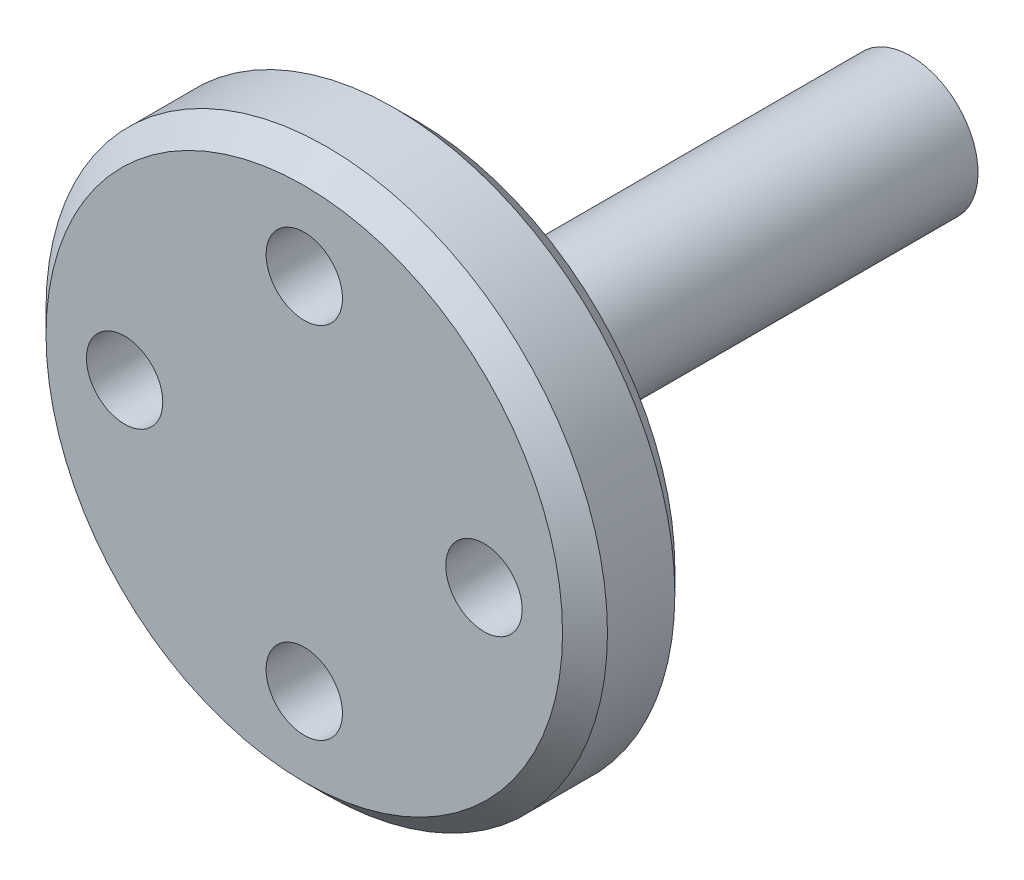
SolidWorks part; units mm, degrees
material "1060 Alloy"
ref_plane "Front Plane" through (0, 0, 0) normal (0, 0, 1) x (1, 0, 0)
ref_plane "Top Plane" through (0, 0, 0) normal (0, 1, 0) x (1, 0, 0)
ref_plane "Right Plane" through (0, 0, 0) normal (1, 0, 0) x (0, 0, -1)
sketch "Sketch1" plane through (0, 0, 0) normal (1, 0, 0) x (0, 0, -1)
  line L0 (0, 0) -> (0, 12.5)
  line L1 (0, 12.5) -> (5, 12.5)
  line L2 (5, 12.5) -> (5, 3)
  line L3 (5, 3) -> (27, 3)
  line L4 (27, 3) -> (27, 0)
  line L5 (27, 0) -> (0, 0)
  dimension "D1" = 12.5
  dimension "D2" = 22
  dimension "D3" = 3
  dimension "D4" = 5
revolve "Revolve1" add sketch "Sketch1" angle 360 about L5
sketch "Sketch2" plane through (0, 0, 0) normal (0, 0, 1) x (1, 0, 0)
  point P0 (8, 0)
  dimension "D1" = 8
hole_wizard "M3 Clearance Hole1" positions "3DSketch1" profile "Sketch3" hole size "M3" standard "ISO"
sketch3d "3DSketch1"
  point P0 (8, 0, 0)
sketch "Sketch3" plane through (8, 0, 0) normal (1, 0, 0) x (0, -1, 0)
  line L0 (0, 0) -> (0, 6.0205)
  line L1 (0, 6.0205) -> (1.7, 4.999)
  line L2 (1.7, 4.999) -> (1.7, 0)
  line L5 (1.7, 0) -> (0, 0)
  line L10 (0, 6.0205) -> (-1.7, 4.999) construction
  line L11 (0, -6.35) -> (0, 107.95) construction
  dimension "Hole Dia." = 3.4
  dimension "Hole Depth" = 4.999
  dimension "Drill Angle" = 118
pattern_circular "CirPattern1" count 4 over 360 about axis through (0, 0, 0) along (0, 0, 1) of "M3 Clearance Hole1"
chamfer "Chamfer1" distance 1 angle 45 2 edges at (0, 12.5, -5) (0, 12.5, 0)
equation "\"L\"= 22mm'length"
equation "\"R\"= 12.5mm'Radius"
equation "\"T\"= 5mm'Thickness"
equation "\"D1@Sketch1\"=\"R\""
equation "\"D2@Sketch1\"=\"L\""
equation "\"SR\"= 3mm'Shaft radius"
equation "\"D3@Sketch1\"=\"SR\""
equation "\"D4@Sketch1\"=\"T\""
